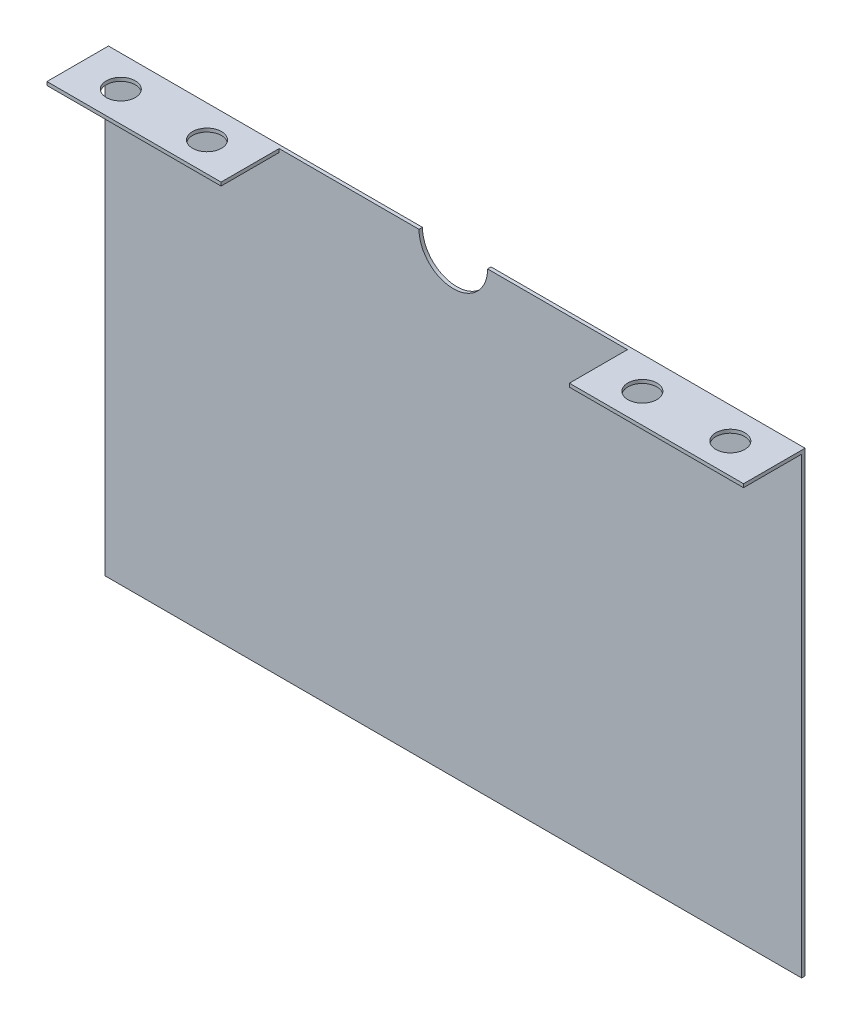
SolidWorks part; units mm, degrees
material "Plain Carbon Steel"
ref_plane "Front Plane" through (0, 0, 0) normal (0, 0, 1) x (1, 0, 0)
ref_plane "Top Plane" through (0, 0, 0) normal (0, 1, 0) x (1, 0, 0)
ref_plane "Right Plane" through (0, 0, 0) normal (1, 0, 0) x (0, 0, -1)
sketch "Sketch1" plane through (0, 0, 0) normal (0, 0, 1) x (1, 0, 0)
  line L0 (0, 0) -> (0, 100) construction
  line L1 (-152.4, 100) -> (-15, 100)
  line L2 (-152.4, 100) -> (-152.4, -100)
  line L3 (-152.4, -100) -> (152.4, -100)
  line L4 (152.4, 100) -> (152.4, -100)
  line L5 (-152.4, 0) -> (152.4, 0) construction
  line L6 (15, 100) -> (152.4, 100)
  line L7 (-15, 100) -> (15, 100) construction
  arc A0 (15, 100) -> (-15, 100) centre (0, 100) cw
  dimension "D3" = 15
  dimension "D1" = 304.8
  dimension "D2" = 200
  dimension "D4" = 152.4
extrude "Bottom Center Casing" add sketch "Sketch1" along normal blind 1.5189
sketch "Sketch2" plane through (0, 0, 1.5189) normal (0, 0, 1) x (1, 0, 0)
  line L0 (-15, 100) -> (-152.4, 100) construction
  line L1 (152.4, 100) -> (15, 100) construction
  line L2 (0, 100) -> (0, 66.7) construction
  line L3 (-83.7, 100) -> (83.7, 100) construction
  point P0 (-83.7, 100)
  point P3 (-83.7, 100)
  point P4 (83.7, 100)
  point P7 (83.7, 100)
  point P12 (0, 100)
  dimension "D1" = 33.3
sketch "Sketch3" plane through (0, 0, 1.5189) normal (0, 0, 1) x (1, 0, 0)
  line L1 (-152.4, 100) -> (-76.2, 100)
  line L2 (-152.4, 100) -> (-152.4, 98.4811)
  line L3 (-152.4, 98.4811) -> (-76.2, 98.4811)
  line L4 (-76.2, 100) -> (-76.2, 98.4811)
  line L5 (152.4, 100) -> (76.2, 100)
  line L6 (152.4, 100) -> (152.4, 98.4811)
  line L7 (152.4, 98.4811) -> (76.2, 98.4811)
  line L8 (76.2, 100) -> (76.2, 98.4811)
  dimension "D1" = 76.2
  dimension "D2" = 1.5189
  dimension "D3" = 1.5189
  dimension "D4" = 76.2
extrude "Boss-Extrude1" add sketch "Sketch3" along normal blind 25.4
sketch "Sketch4" plane through (0, 100, 0) normal (0, 1, 0) x (1, 0, 0)
  line L0 (-152.4, -13.4595) -> (-76.2, -14.2189) construction
  line L1 (-152.4, -26.9189) -> (-152.4, 0) construction
  line L2 (-76.2, -26.9189) -> (-76.2, -1.5189) construction
  line L4 (0, -14.8054) -> (0, 14.8054) construction
  circle A0 centre (-133.35, -13.6493) radius 6.35
  circle A1 centre (-95.25, -14.0291) radius 6.35
  circle A2 centre (95.25, -14.0291) radius 6.35
  circle A3 centre (133.35, -13.6493) radius 6.35
  dimension "D1" = 12.7
  dimension "D2" = 19.05
  dimension "D3" = 38.1
extrude "Cut-Extrude1" cut sketch "Sketch4" against normal blind 25.4
